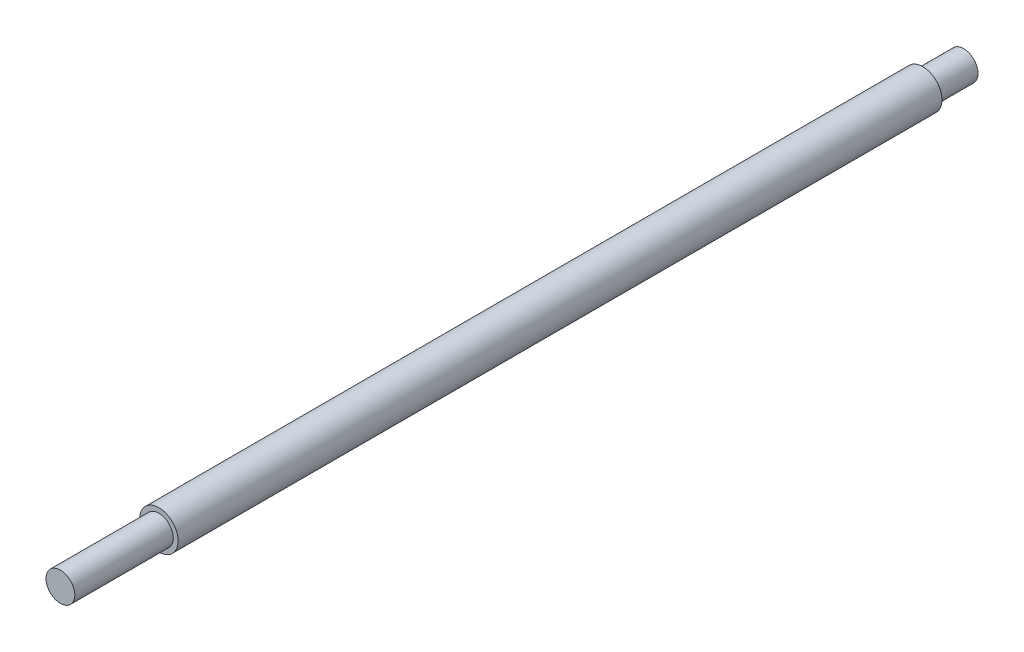
SolidWorks part; units mm, degrees
material "7079 Alloy"
ref_plane "Front" through (0, 0, 0) normal (0, 0, 1) x (1, 0, 0)
ref_plane "Top" through (0, 0, 0) normal (0, 1, 0) x (1, 0, 0)
ref_plane "Right" through (0, 0, 0) normal (1, 0, 0) x (0, 0, -1)
sketch "Sketch1" plane through (0, 0, 0) normal (0, 0, 1) x (1, 0, 0)
  circle A0 centre (0, 0) radius 8
extrude "Extrude1" add sketch "Sketch1" along normal blind 366
sketch "Sketch3" plane through (0, 0, 366) normal (0, 0, 1) x (1, 0, 0)
  circle A0 centre (0, 0) radius 6
  circle A1 centre (0, 0) radius 8
  circle M1 centre (0, 0) radius 8
extrude "Cut-Extrude1" cut sketch "Sketch3" against normal blind 34 contours A0 M1
sketch "Sketch4" plane through (0, 0, 0) normal (0, 0, -1) x (-1, 0, 0)
  circle A0 centre (0, 0) radius 6
  circle A1 centre (0, 0) radius 8
  circle M1 centre (0, 0) radius 8
extrude "Cut-Extrude2" cut sketch "Sketch4" against normal blind 20 contours A0 M1
sketch "Sketch5" plane through (0, 0, 366) normal (0, 0, 1) x (1, 0, 0)
  circle A0 centre (0, 0) radius 6
extrude "Extrude2" add sketch "Sketch5" along normal blind 10
sketch "Sketch7" plane through (0, 0, 332) normal (0, 0, 1) x (1, 0, 0)
  circle A0 centre (0, 0) radius 8
  circle A1 centre (0, 0) radius 6
extrude "Extrude3" add sketch "Sketch7" along normal blind 3
sketch "Sketch8" plane through (0, 0, 20) normal (0, 0, -1) x (-1, 0, 0)
  circle A0 centre (0, 0) radius 8
  circle A1 centre (0, 0) radius 6
extrude "Extrude4" add sketch "Sketch8" along normal blind 3
